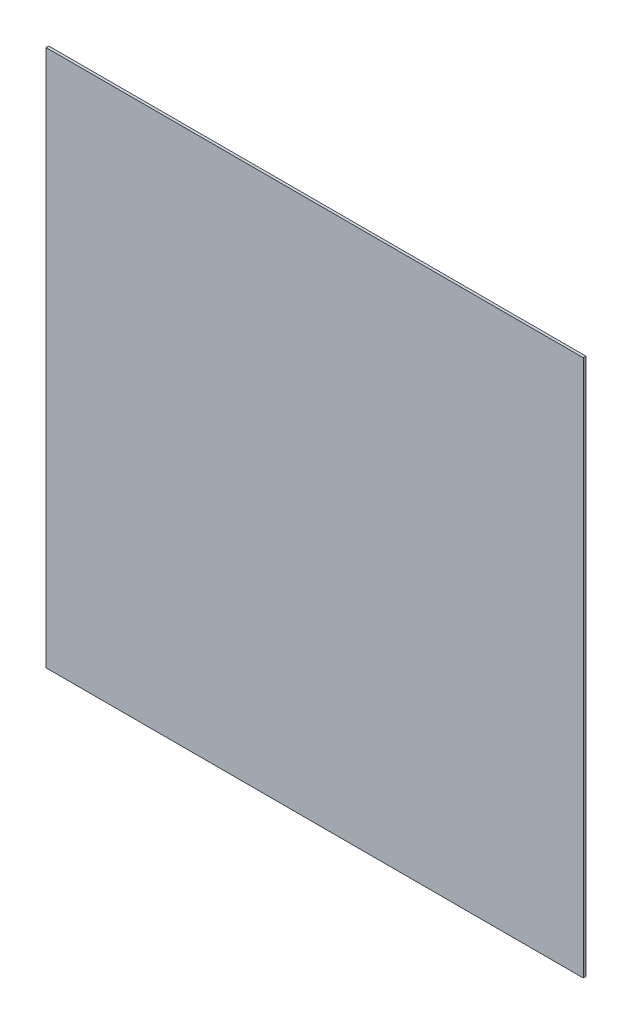
SolidWorks part; units mm, degrees
ref_plane "Plan de face" through (0, 0, 0) normal (0, 0, 1) x (1, 0, 0)
ref_plane "Plan de dessus" through (0, 0, 0) normal (0, 1, 0) x (1, 0, 0)
ref_plane "Plan de droite" through (0, 0, 0) normal (1, 0, 0) x (0, 0, -1)
sketch "Esquisse1" plane through (0, 0, 0) normal (0, 0, 1) x (1, 0, 0)
  line L1 (0, 0) -> (-600, 0)
  line L2 (0, 0) -> (0, 600)
  line L3 (0, 600) -> (-600, 600)
  line L4 (-600, 0) -> (-600, 600)
  dimension "D1" = 600
extrude "Boss.-Extru.1" add sketch "Esquisse1" along normal blind 3
